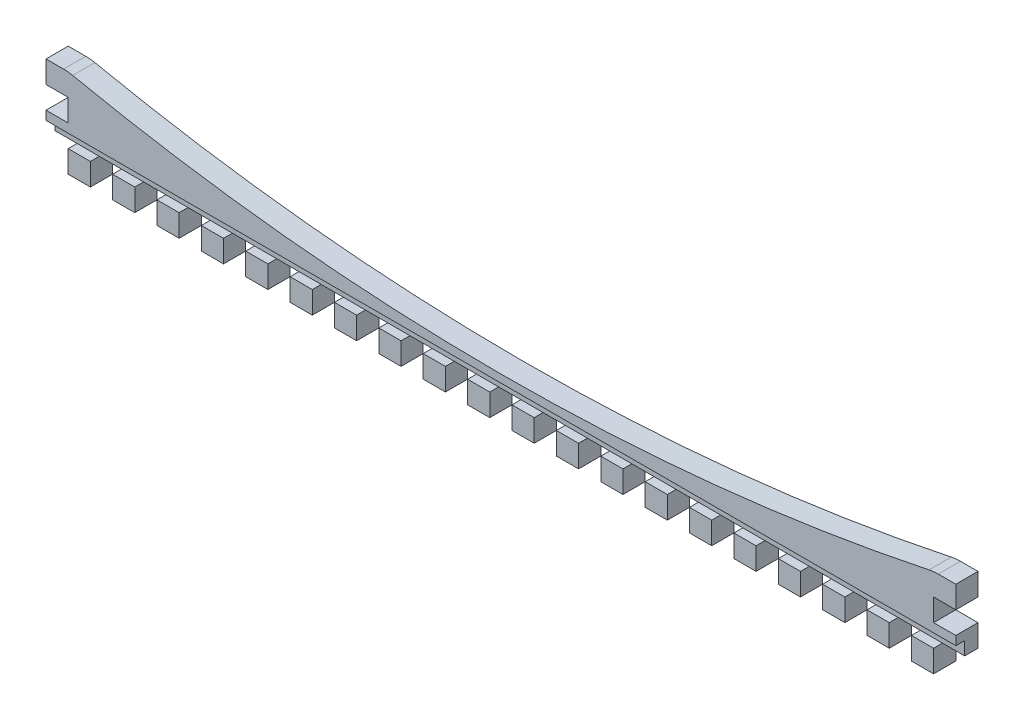
SolidWorks part; units mm, degrees
ref_plane "Plan de face" through (0, 0, 0) normal (0, 0, 1) x (1, 0, 0)
ref_plane "Plan de dessus" through (0, 0, 0) normal (0, 1, 0) x (1, 0, 0)
ref_plane "Plan de droite" through (0, 0, 0) normal (1, 0, 0) x (0, 0, -1)
sketch "Esquisse1" plane through (0, 0, 0) normal (0, 0, 1) x (1, 0, 0)
  line L1 (-46.0095, -29.453) -> (158.9905, -29.453)
  line L2 (-46.0095, -29.453) -> (-46.0095, -49.453)
  line L3 (-46.0095, -49.453) -> (158.9905, -49.453)
  line L4 (158.9905, -29.453) -> (158.9905, -49.453)
extrude "Boss.-Extru.1" add sketch "Esquisse1" along normal blind 5
sketch "Esquisse2" plane through (0, 0, 5) normal (0, 0, 1) x (1, 0, 0)
  line L0 (148.9905, -49.453) -> (143.9905, -49.453)
  line L1 (158.9905, -49.453) -> (153.9905, -49.453)
  line L2 (158.9905, -49.453) -> (158.9905, -44.453)
  line L3 (158.9905, -44.453) -> (153.9905, -44.453)
  line L4 (153.9905, -49.453) -> (153.9905, -44.453)
  line L5 (148.9905, -49.453) -> (148.9905, -44.453)
  line L6 (148.9905, -44.453) -> (143.9905, -44.453)
  line L7 (143.9905, -49.453) -> (143.9905, -44.453)
  line L8 (138.9905, -49.453) -> (133.9905, -49.453)
  line L9 (138.9905, -49.453) -> (138.9905, -44.453)
  line L10 (138.9905, -44.453) -> (133.9905, -44.453)
  line L11 (133.9905, -49.453) -> (133.9905, -44.453)
  line L12 (128.9905, -49.453) -> (123.9905, -49.453)
  line L13 (128.9905, -49.453) -> (128.9905, -44.453)
  line L14 (128.9905, -44.453) -> (123.9905, -44.453)
  line L15 (123.9905, -49.453) -> (123.9905, -44.453)
  line L16 (118.9905, -49.453) -> (113.9905, -49.453)
  line L17 (118.9905, -49.453) -> (118.9905, -44.453)
  line L18 (118.9905, -44.453) -> (113.9905, -44.453)
  line L19 (113.9905, -49.453) -> (113.9905, -44.453)
  line L20 (108.9905, -49.453) -> (103.9905, -49.453)
  line L21 (108.9905, -49.453) -> (108.9905, -44.453)
  line L22 (108.9905, -44.453) -> (103.9905, -44.453)
  line L23 (103.9905, -49.453) -> (103.9905, -44.453)
  line L24 (98.9905, -49.453) -> (93.9905, -49.453)
  line L25 (98.9905, -49.453) -> (98.9905, -44.453)
  line L26 (98.9905, -44.453) -> (93.9905, -44.453)
  line L27 (93.9905, -49.453) -> (93.9905, -44.453)
  line L28 (88.9905, -49.453) -> (83.9905, -49.453)
  line L29 (88.9905, -49.453) -> (88.9905, -44.453)
  line L30 (88.9905, -44.453) -> (83.9905, -44.453)
  line L31 (83.9905, -49.453) -> (83.9905, -44.453)
  line L32 (78.9905, -49.453) -> (73.9905, -49.453)
  line L33 (78.9905, -49.453) -> (78.9905, -44.453)
  line L34 (78.9905, -44.453) -> (73.9905, -44.453)
  line L35 (73.9905, -49.453) -> (73.9905, -44.453)
  line L36 (68.9905, -49.453) -> (63.9905, -49.453)
  line L37 (68.9905, -49.453) -> (68.9905, -44.453)
  line L38 (68.9905, -44.453) -> (63.9905, -44.453)
  line L39 (63.9905, -49.453) -> (63.9905, -44.453)
  line L40 (58.9905, -49.453) -> (53.9905, -49.453)
  line L41 (58.9905, -49.453) -> (58.9905, -44.453)
  line L42 (58.9905, -44.453) -> (53.9905, -44.453)
  line L43 (53.9905, -49.453) -> (53.9905, -44.453)
  line L44 (48.9905, -49.453) -> (43.9905, -49.453)
  line L45 (48.9905, -49.453) -> (48.9905, -44.453)
  line L46 (48.9905, -44.453) -> (43.9905, -44.453)
  line L47 (43.9905, -49.453) -> (43.9905, -44.453)
  line L48 (38.9905, -49.453) -> (33.9905, -49.453)
  line L49 (38.9905, -49.453) -> (38.9905, -44.453)
  line L50 (38.9905, -44.453) -> (33.9905, -44.453)
  line L51 (33.9905, -49.453) -> (33.9905, -44.453)
  line L52 (28.9905, -49.453) -> (23.9905, -49.453)
  line L53 (28.9905, -49.453) -> (28.9905, -44.453)
  line L54 (28.9905, -44.453) -> (23.9905, -44.453)
  line L55 (23.9905, -49.453) -> (23.9905, -44.453)
  line L56 (18.9905, -49.453) -> (13.9905, -49.453)
  line L57 (18.9905, -49.453) -> (18.9905, -44.453)
  line L58 (18.9905, -44.453) -> (13.9905, -44.453)
  line L59 (13.9905, -49.453) -> (13.9905, -44.453)
  line L60 (8.9905, -49.453) -> (3.9905, -49.453)
  line L61 (8.9905, -49.453) -> (8.9905, -44.453)
  line L62 (8.9905, -44.453) -> (3.9905, -44.453)
  line L63 (3.9905, -49.453) -> (3.9905, -44.453)
  line L64 (-1.0095, -49.453) -> (-6.0095, -49.453)
  line L65 (-1.0095, -49.453) -> (-1.0095, -44.453)
  line L66 (-1.0095, -44.453) -> (-6.0095, -44.453)
  line L67 (-6.0095, -49.453) -> (-6.0095, -44.453)
  line L68 (-11.0095, -49.453) -> (-16.0095, -49.453)
  line L69 (-11.0095, -49.453) -> (-11.0095, -44.453)
  line L70 (-11.0095, -44.453) -> (-16.0095, -44.453)
  line L71 (-16.0095, -49.453) -> (-16.0095, -44.453)
  line L72 (-21.0095, -49.453) -> (-26.0095, -49.453)
  line L73 (-21.0095, -49.453) -> (-21.0095, -44.453)
  line L74 (-21.0095, -44.453) -> (-26.0095, -44.453)
  line L75 (-26.0095, -49.453) -> (-26.0095, -44.453)
  line L76 (-31.0095, -49.453) -> (-36.0095, -49.453)
  line L77 (-31.0095, -49.453) -> (-31.0095, -44.453)
  line L78 (-31.0095, -44.453) -> (-36.0095, -44.453)
  line L79 (-36.0095, -49.453) -> (-36.0095, -44.453)
  line L80 (158.9905, -39.453) -> (153.9905, -39.453)
  line L81 (158.9905, -39.453) -> (158.9905, -34.453)
  line L82 (158.9905, -34.453) -> (153.9905, -34.453)
  line L83 (153.9905, -39.453) -> (153.9905, -34.453)
  line L88 (158.9905, -29.453) -> (-46.0095, -29.453) construction
  line L89 (-41.0095, -29.453) -> (153.9905, -29.453)
  line L96 (-41.0095, -49.453) -> (-46.0095, -49.453)
  line L97 (-41.0095, -49.453) -> (-41.0095, -44.453)
  line L98 (-41.0095, -44.453) -> (-46.0095, -44.453)
  line L99 (-46.0095, -49.453) -> (-46.0095, -44.453)
  line L100 (-41.0095, -39.453) -> (-46.0095, -39.453)
  line L101 (-41.0095, -39.453) -> (-41.0095, -34.453)
  line L102 (-41.0095, -34.453) -> (-46.0095, -34.453)
  line L103 (-46.0095, -39.453) -> (-46.0095, -34.453)
  arc A0 (-41.0095, -29.453) -> (153.9905, -29.453) centre (56.4905, 429.5127) ccw
  dimension "D1" = 21
  dimension "D3" = 2
  dimension "D2" = 2
extrude "Enlèv. mat.-Extru.2" cut sketch "Esquisse2" along direction (0, 0, 1) on the side against the normal up to surface (5 mm away)
sketch "Esquisse3" plane through (0, 0, 5) normal (0, 0, 1) x (1, 0, 0)
  line L1 (-46.0095, -44.453) -> (158.9905, -44.453)
  line L2 (-46.0095, -44.453) -> (-46.0095, -41.453)
  line L3 (-46.0095, -41.453) -> (158.9905, -41.453)
  line L4 (158.9905, -44.453) -> (158.9905, -41.453)
extrude "Enlèv. mat.-Extru.3" cut sketch "Esquisse3" against normal blind 2
ref_plane "Plan1" through (-46.0095, -41.453, 5) normal (-1, 0, 0) x (0, 0, 1)
fillet "Congé2" radius 10 1 edges at (153.9905, -29.453, 2.5)
fillet "Congé3" radius 10 1 edges at (-41.0095, -29.453, 2.5)
